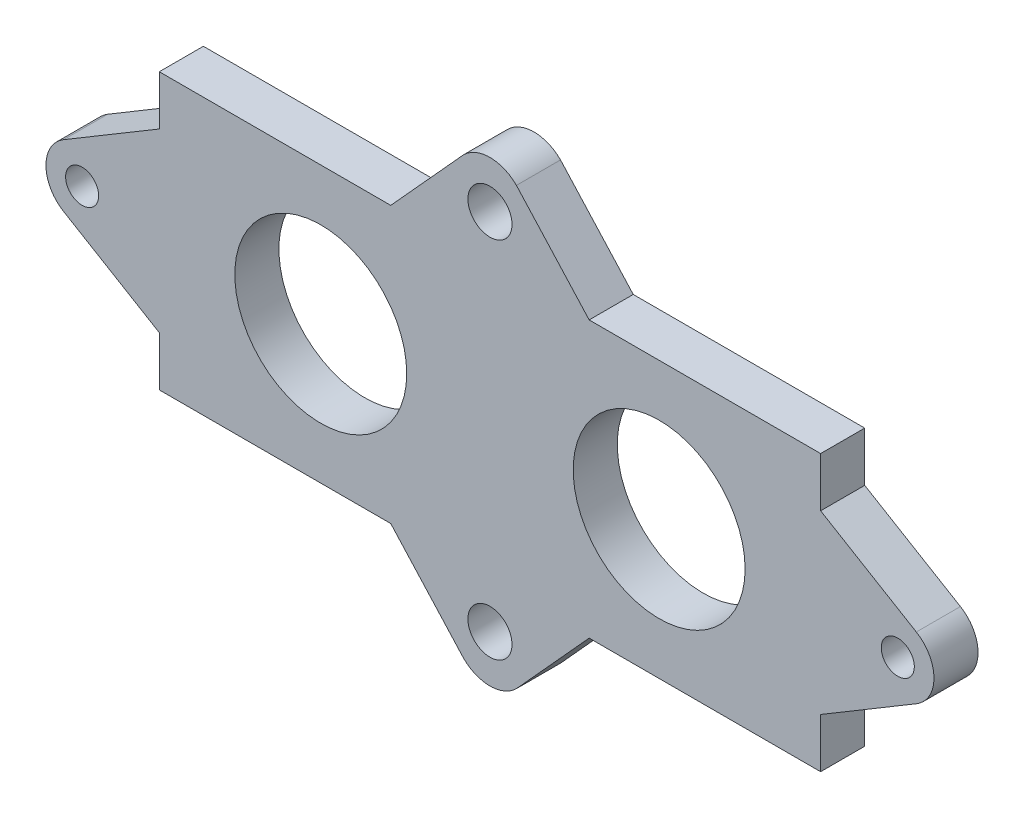
SolidWorks part; units mm, degrees
ref_plane "Front" through (0, 0, 0) normal (0, 0, 1) x (1, 0, 0)
ref_plane "Top" through (0, 0, 0) normal (0, 1, 0) x (1, 0, 0)
ref_plane "Right" through (0, 0, 0) normal (1, 0, 0) x (0, 0, -1)
sketch "Sketch1" plane through (0, 0, 0) normal (0, 0, 1) x (1, 0, 0)
  line L0 (-9, 12.5) -> (-2.401, 19.7724)
  line L1 (-30, 12.5) -> (-9, 12.5)
  line L2 (-30, 12.5) -> (-30, 8)
  line L4 (30, 12.5) -> (30, 8)
  line L5 (2.401, 19.7724) -> (9, 12.5)
  line L6 (9, 12.5) -> (30, 12.5)
  line L7 (-52.4135, 0) -> (76.2531, 0) construction
  line L12 (9, -12.5) -> (30, -12.5)
  line L13 (2.401, -19.7724) -> (9, -12.5)
  line L14 (-30, -12.5) -> (-9, -12.5)
  line L15 (-9, -12.5) -> (-2.401, -19.7724)
  line L16 (-30, -8) -> (-38.6825, -2.8203)
  line L17 (-38.6825, 2.8203) -> (-30, 8)
  line L18 (-30, -8) -> (-30, -12.5)
  line L19 (0, 44.7347) -> (0, -34.4115) construction
  line L20 (38.6825, 2.8203) -> (30, 8)
  line L21 (30, -8) -> (38.6825, -2.8203)
  line L22 (30, -8) -> (30, -12.5)
  circle A0 centre (-15.35, 0) radius 7.8
  circle A1 centre (15.35, 0) radius 7.8
  circle A2 centre (0, 16.5) radius 2
  arc A4 (-2.401, 19.7724) -> (2.401, 19.7724) centre (0, 17.3714) cw
  arc A5 (-2.401, -19.7724) -> (2.401, -19.7724) centre (0, -17.3714) ccw
  circle A6 centre (0, -16.5) radius 2
  circle A7 centre (-37, 0) radius 1.5
  arc A8 (-38.6825, -2.8203) -> (-38.6825, 2.8203) centre (-37, 0) cw
  arc A9 (38.6825, -2.8203) -> (38.6825, 2.8203) centre (37, 0) ccw
  circle A10 centre (37, 0) radius 1.5
  dimension "D3" = 15.6
  dimension "D4" = 15.6
  dimension "D9" = 4
  dimension "D10" = 8
  dimension "D5" = 3
  dimension "D6" = 7
  dimension "D1" = 60
  dimension "D2" = 25
  dimension "D7" = 21
  dimension "D8" = 21
  dimension "D11" = 8
extrude "Boss-Extrude1" add sketch "Sketch1" along normal blind 4
